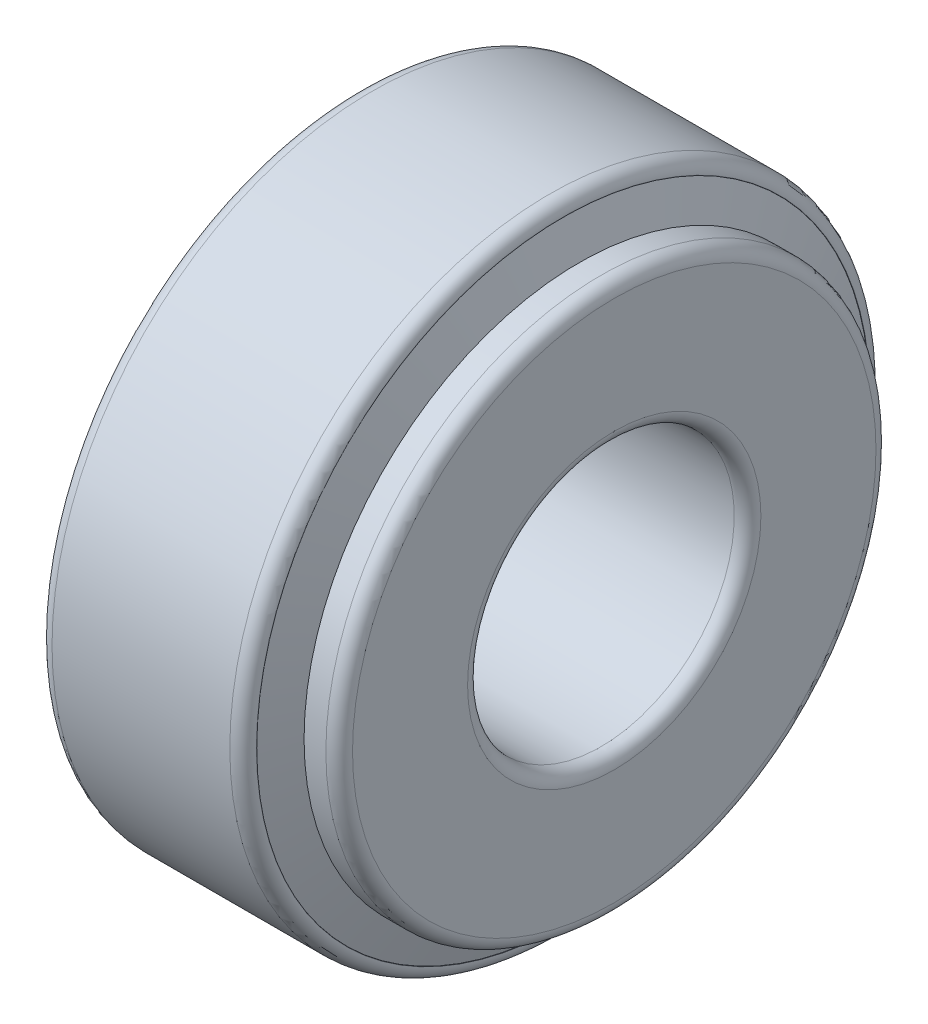
SolidWorks part; units mm, degrees
material "AISI Тип A2 Инструментальная сталь"
ref_plane "Спереди" through (0, 0, 0) normal (0, 0, 1) x (1, 0, 0)
ref_plane "Сверху" through (0, 0, 0) normal (0, 1, 0) x (1, 0, 0)
ref_plane "Справа" through (0, 0, 0) normal (1, 0, 0) x (0, 0, -1)
sketch "Эскиз1" plane through (0, 0, 0) normal (0, 0, 1) x (1, 0, 0)
  line L20 (-882.5277, 0) -> (43243.8573, 0) construction
  line L33 (3.1089, 26.5041) -> (0, 25.259)
  line L34 (0, 25.259) -> (0, 34.5)
  line L35 (1.5, 36) -> (21.5, 36)
  line L36 (23, 34.5) -> (23, 34.4702)
  line L37 (23, 34.4702) -> (22.9723, 34.4591)
  line L38 (3.1089, 26.5041) -> (22.9723, 34.4591) construction
  line L39 (4.4678, 22.7705) -> (1.75, 22.7705)
  line L40 (1.75, 22.7705) -> (1.75, 16.5)
  line L41 (3.25, 15) -> (27.25, 15)
  line L42 (28.75, 16.5) -> (28.75, 29.4446)
  line L43 (27.25, 30.9446) -> (24.7975, 30.9446)
  line L44 (24.7975, 30.9446) -> (24.7975, 29.4446)
  line L45 (4.4678, 22.7705) -> (24.7975, 29.4446) construction
  line L46 (24.7975, 29.4446) -> (22.9723, 34.4591)
  line L47 (4.4678, 22.7705) -> (3.1089, 26.5041)
  line L48 (3.7883, 24.6373) -> (23.8849, 31.9518) construction
  line L50 (3.1089, 26.5041) -> (3.1089, 22.7705) construction
  arc A0 (0, 34.5) -> (1.5, 36) centre (1.5, 34.5) cw
  arc A1 (21.5, 36) -> (23, 34.5) centre (21.5, 34.5) cw
  arc A2 (1.75, 16.5) -> (3.25, 15) centre (3.25, 16.5) ccw
  arc A3 (28.75, 16.5) -> (27.25, 15) centre (27.25, 16.5) cw
  arc A4 (27.25, 30.9446) -> (28.75, 29.4446) centre (27.25, 29.4446) cw
  point P12 (23.8849, 31.9518)
  dimension "гост r2" = 1.5
  dimension "гост r1" = 1.5
  dimension "гост E" = 50.518
  dimension "гост C" = 23
  dimension "гост DD" = 72
  dimension "гост B" = 27
  dimension "гост T" = 28.75
  dimension "гост d" = 30
  dimension "гост alfa" = 20
  dimension "D1" = 29.4446
  dimension "D2" = 22.7705
  dimension "D3" = 5.3363
  dimension "D4" = 3.9731
  dimension "D5" = 0.0298
revolve "Повернуть1" add sketch "Эскиз1" angle 360 about L20
equation "\"D4@Эскиз1\"=\"D3@Эскиз1\"*(\"D2@Эскиз1\"/\"D1@Эскиз1\")"
